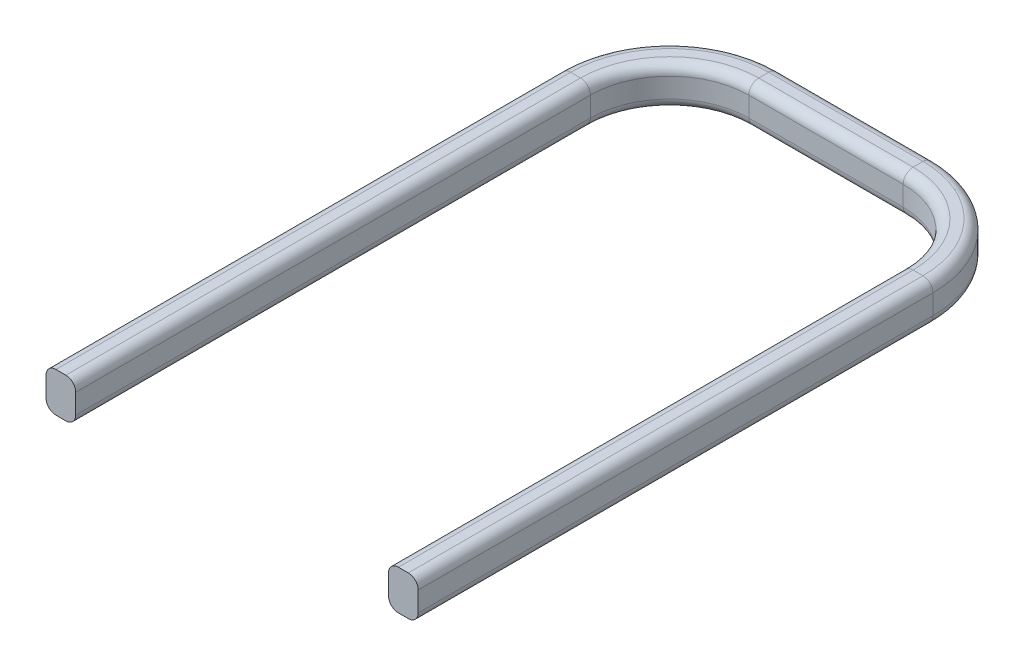
SolidWorks part; units mm, degrees
ref_plane "Front Plane" through (0, 0, 0) normal (0, 0, 1) x (1, 0, 0)
ref_plane "Top Plane" through (0, 0, 0) normal (0, 1, 0) x (1, 0, 0)
ref_plane "Right Plane" through (0, 0, 0) normal (1, 0, 0) x (0, 0, -1)
sketch "Sketch1" plane through (0, 0, 0) normal (0, 1, 0) x (1, 0, 0)
  line L0 (-3.95, 0) -> (-3.95, 13)
  line L1 (-1.95, 15) -> (1.95, 15)
  line L2 (3.95, 13) -> (3.95, 0)
  arc A0 (1.95, 15) -> (3.95, 13) centre (1.95, 13) cw
  arc A1 (-3.95, 13) -> (-1.95, 15) centre (-1.95, 13) cw
  point P5 (0, 15)
  point P11 (-3.95, 15)
  dimension "D3" = 2
  dimension "D1" = 3.95
  dimension "D2" = 15
sketch "Sketch2" plane through (0, 0, 0) normal (0, 0, 1) x (1, 0, 0)
  line L1 (-3.95, 0) -> (-4.7, 0)
  line L2 (-3.95, 0) -> (-3.95, 1)
  line L3 (-3.95, 1) -> (-4.7, 1)
  line L4 (-4.7, 0) -> (-4.7, 1)
  dimension "D1" = 1
  dimension "D2" = 0.75
sweep "Sweep1" add profiles "Sketch2" path "Sketch1"
fillet "Fillet1" radius 0.25 20 edges at (4.7, 0, -6.5) (3.8945, 0, -14.9445) (0, 0, -15.75) (-3.8945, 0, -14.9445) (3.95, 0, -6.5) (3.3642, 0, -14.4142) (0, 0, -15) (-3.3642, 0, -14.4142) (4.7, 1, -6.5) (3.8945, 1, -14.9445) (0, 1, -15.75) (-3.8945, 1, -14.9445) (3.95, 1, -6.5) (3.3642, 1, -14.4142) (0, 1, -15) (-3.3642, 1, -14.4142) (-4.7, 0, -6.5) (-3.95, 0, -6.5) (-4.7, 1, -6.5) (-3.95, 1, -6.5)
scale "Scale1" scale about centroid uniform scaling yes scale factor 10
